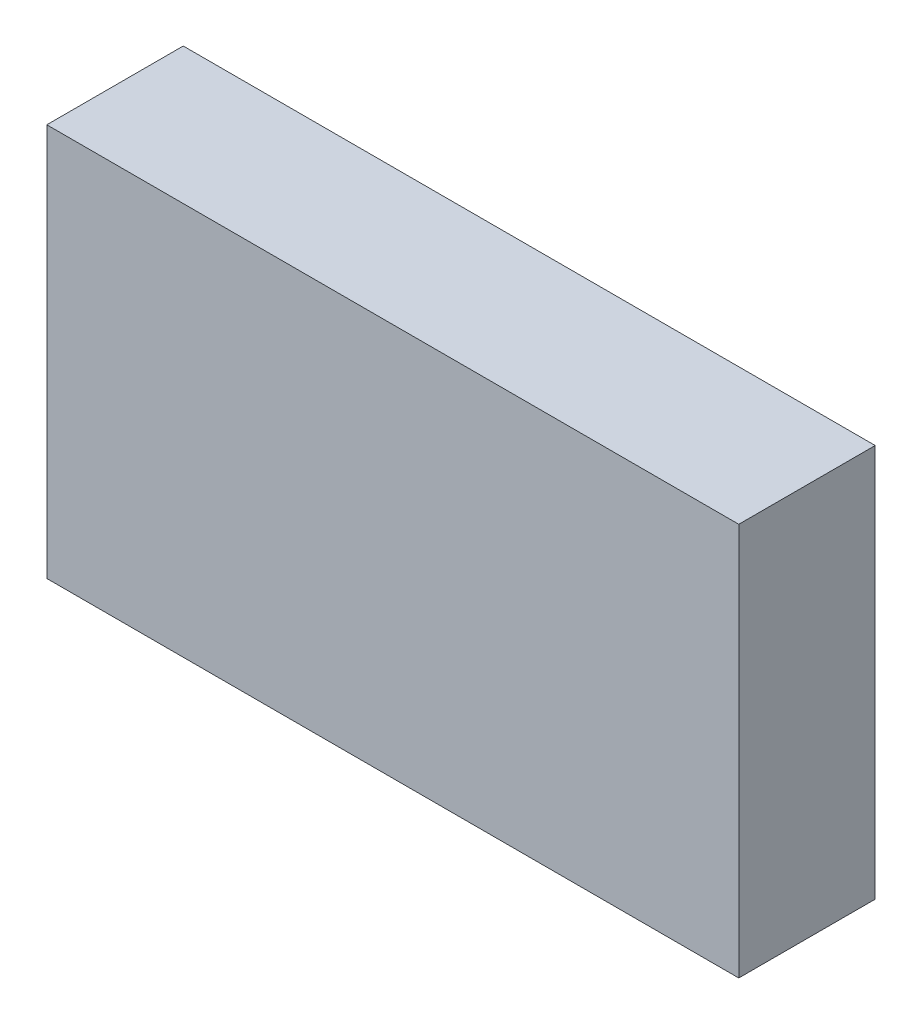
SolidWorks part; units mm, degrees
ref_plane "Front Plane" through (0, 0, 0) normal (0, 0, 1) x (1, 0, 0)
ref_plane "Top Plane" through (0, 0, 0) normal (0, 1, 0) x (1, 0, 0)
ref_plane "Right Plane" through (0, 0, 0) normal (1, 0, 0) x (0, 0, -1)
sketch "Sketch1" plane through (0, 0, 0) normal (0, 0, 1) x (1, 0, 0)
  line L1 (-63.395, -36) -> (63.395, -36)
  line L2 (-63.395, -36) -> (-63.395, 36)
  line L3 (-63.395, 36) -> (63.395, 36)
  line L4 (63.395, -36) -> (63.395, 36)
  line L5 (-63.395, -36) -> (63.395, 36) construction
  line L6 (-63.395, 36) -> (63.395, -36) construction
  point P0 (0, 0)
  dimension "D1" = 126.79
  dimension "D2" = 72
extrude "Boss-Extrude1" add sketch "Sketch1" along normal blind 25
